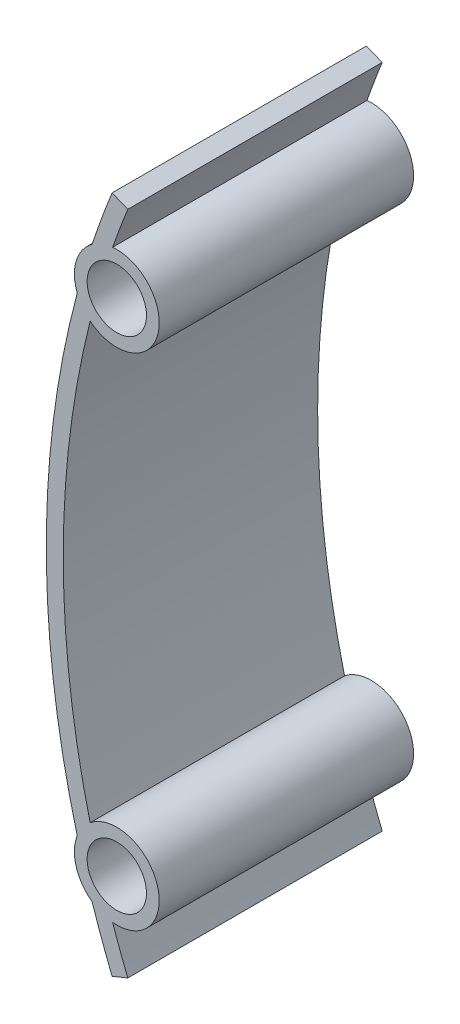
SolidWorks part; units mm, degrees
ref_plane "Front Plane" through (0, 0, 0) normal (0, 0, 1) x (1, 0, 0)
ref_plane "Top Plane" through (0, 0, 0) normal (0, 1, 0) x (1, 0, 0)
ref_plane "Right Plane" through (0, 0, 0) normal (1, 0, 0) x (0, 0, -1)
sketch "Sketch1" plane through (0, 0, 0) normal (0, 0, 1) x (1, 0, 0)
  line L0 (107, 0) -> (0, 0) construction
  line L1 (7.7579, 40) -> (7.7579, -40) construction
  line L2 (9.6129, 39.2523) -> (9.6129, -39.2523) construction
  line L3 (7.7579, 40) -> (9.6129, 39.2523)
  line L4 (9.6129, 39.2523) -> (107, 0) construction
  line L5 (7.7579, -40) -> (9.6129, -39.2523)
  line L6 (9.6129, -39.2523) -> (107, 0) construction
  line L7 (8.3149, 29.5) -> (8.3149, -29.5) construction
  arc A0 (7.7579, 40) -> (5.4, 33.5624) centre (107, 0) ccw
  arc A1 (9.6129, 39.2523) -> (7.8212, 34.4756) centre (107, 0) ccw
  circle A2 centre (8.3149, 29.5) radius 3.5
  circle A3 centre (8.3149, -29.5) radius 3.5
  circle A4 centre (107, 0) radius 103 construction
  arc A5 (5.4, 33.5624) -> (3.6487, 27.7038) centre (8.3149, 29.5) ccw
  arc A6 (3.6487, -27.7038) -> (5.4, -33.5624) centre (8.3149, -29.5) ccw
  arc A7 (5.1715, 25.6117) -> (5.1715, -25.6117) centre (107, 0) ccw
  arc A8 (5.1715, 25.6117) -> (7.8212, 34.4756) centre (8.3149, 29.5) ccw
  arc A9 (3.6487, 27.7038) -> (3.6487, -27.7038) centre (107, 0) ccw
  arc A11 (7.8212, -34.4756) -> (9.6129, -39.2523) centre (107, 0) ccw
  arc A12 (7.8212, -34.4756) -> (5.1715, -25.6117) centre (8.3149, -29.5) ccw
  arc A13 (5.4, -33.5624) -> (7.7579, -40) centre (107, 0) ccw
  dimension "D1" = 214
  dimension "D5" = 206
  dimension "D6" = 7
  dimension "D7" = 10
  dimension "D8" = 5
  dimension "D2" = 80
  dimension "D3" = 2
  dimension "D4" = 59
extrude "Boss-Extrude1" add sketch "Sketch1" along normal blind 30
